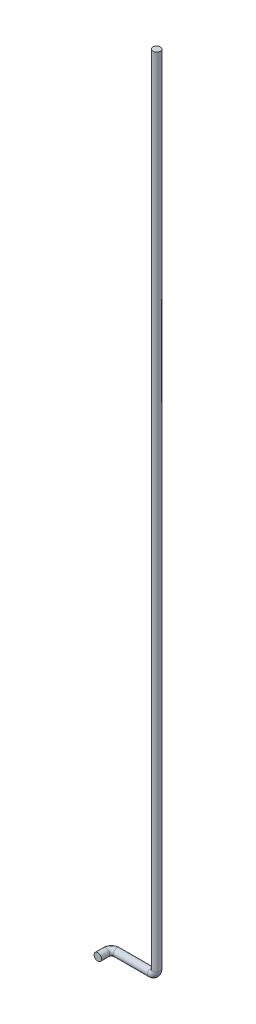
SolidWorks part; units mm, degrees
ref_plane "Alzado" through (0, 0, 0) normal (0, 0, 1) x (1, 0, 0)
ref_plane "Planta" through (0, 0, 0) normal (0, 1, 0) x (1, 0, 0)
ref_plane "Vista lateral" through (0, 0, 0) normal (1, 0, 0) x (0, 0, -1)
sketch3d "Croquis3D1"
  line L0 (0, 0, 0) -> (0, -2925, 0)
  line L1 (-20, -2945, 0) -> (-146, -2945, 0)
  line L2 (-166, -2945, 20) -> (-166, -2945, 50)
  arc A0 (-146, -2945, 0) -> (-166, -2945, 20) centre (-146, -2945, 20) ccw
  arc A1 (0, -2925, 0) -> (-20, -2945, 0) centre (-20, -2925, 0) ccw
  point P7 (-166, -2945, 0)
  point P8 (-146, -2925, 20)
  point P11 (0, -2945, 0)
  point P12 (-20, -2925, -20)
  dimension "D4" = 20
  dimension "D1" = 2945
  dimension "D2" = 166
  dimension "D3" = 50
sketch "Croquis1" plane through (0, 0, 0) normal (0, 1, 0) x (1, 0, 0)
  circle A0 centre (0, 0) radius 13.7
  dimension "D1" = 27.4
sweep "Barrer1" add profiles "Croquis1" path "Croquis3D1"
